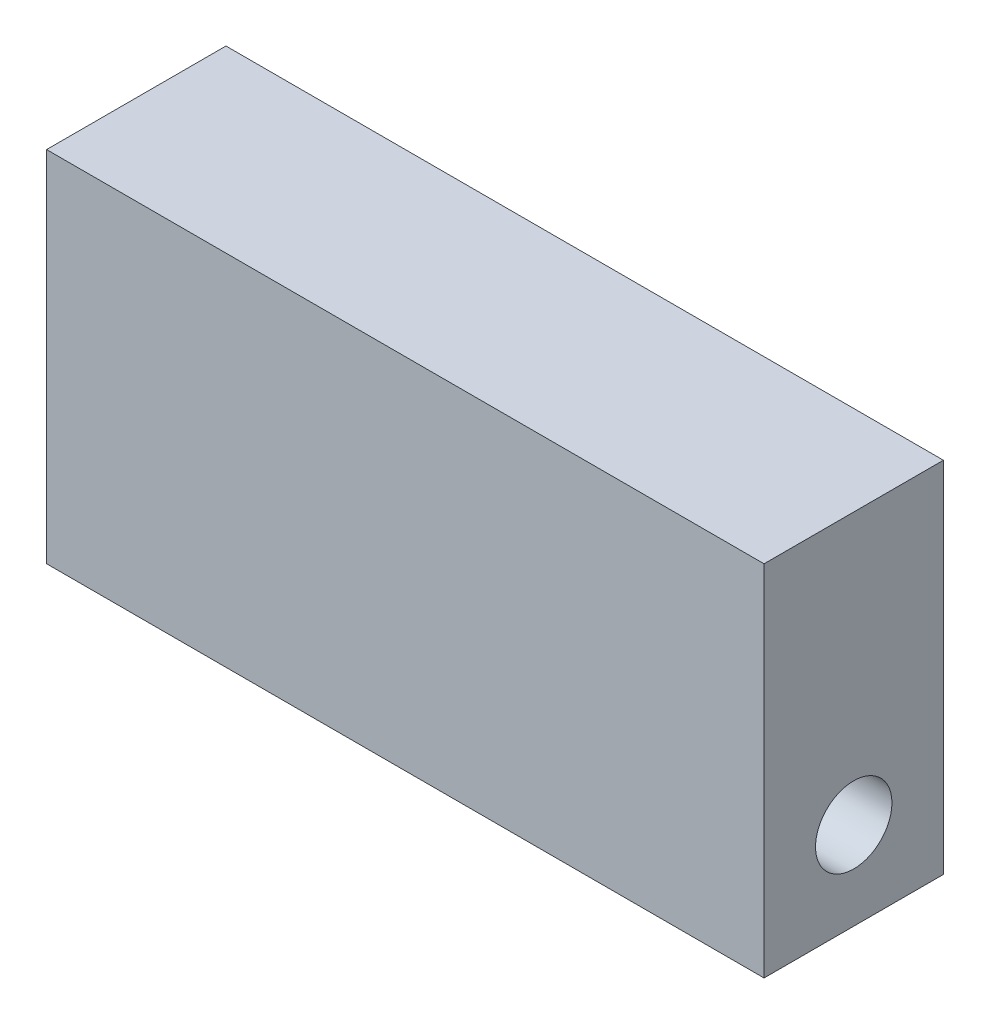
SolidWorks part; units mm, degrees
material "6061-T6 (SS)"
ref_plane "Front Plane" through (0, 0, 0) normal (0, 0, 1) x (1, 0, 0)
ref_plane "Top Plane" through (0, 0, 0) normal (0, 1, 0) x (1, 0, 0)
ref_plane "Right Plane" through (0, 0, 0) normal (1, 0, 0) x (0, 0, -1)
sketch "Sketch1" plane through (0, 0, 0) normal (0, 1, 0) x (1, 0, 0)
  line L1 (-25.4, -6.35) -> (25.4, -6.35)
  line L2 (-25.4, -6.35) -> (-25.4, 6.35)
  line L3 (-25.4, 6.35) -> (25.4, 6.35)
  line L4 (25.4, -6.35) -> (25.4, 6.35)
  line L5 (-25.4, -6.35) -> (25.4, 6.35) construction
  line L6 (-25.4, 6.35) -> (25.4, -6.35) construction
  point P0 (0, 0)
  dimension "D1" = 50.8
  dimension "D2" = 12.7
extrude "Boss-Extrude1" add sketch "Sketch1" along normal blind 25.4
hole_wizard "1/4-28 Tapped Hole1" positions "Sketch2" profile "Sketch3" tap size "1/4-28" standard "ANSI Inch"
sketch "Sketch2" plane through (25.4, 0, 0) normal (1, 0, 0) x (0, 0, -1)
  point P0 (0, 6.2152)
sketch "Sketch3" plane through (25.4, 6.2152, 0) normal (0, 1, 0) x (0, 0, -1)
  line L0 (0, 0) -> (0, 31.5974)
  line L1 (0, 31.5974) -> (2.7051, 29.972)
  line L2 (2.7051, 29.972) -> (2.7051, 0)
  line L5 (2.7051, 0) -> (0, 0)
  line L10 (0, 31.5974) -> (-2.7051, 29.972) construction
  line L11 (0, -6.35) -> (0, 107.95) construction
  dimension "Tap Drill Dia." = 5.4102
  dimension "Tap Drill Depth" = 29.972
  dimension "Drill Angle" = 118
cosmetic thread "Hole Thread1" parameters "D1"=25.4, "D2"=6.35
